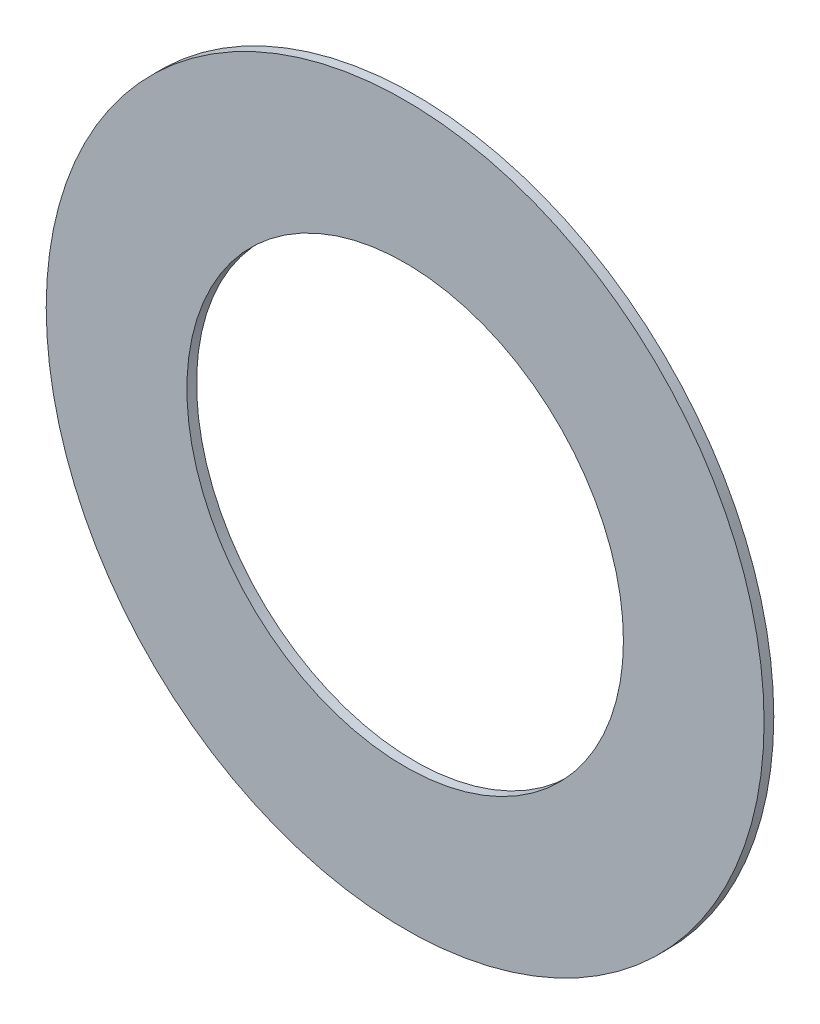
SolidWorks part; units mm, degrees
material "А1 ГОСТ 9347-74"
ref_plane "Спереди" through (0, 0, 0) normal (0, 0, 1) x (1, 0, 0)
ref_plane "Сверху" through (0, 0, 0) normal (0, 1, 0) x (1, 0, 0)
ref_plane "Справа" through (0, 0, 0) normal (1, 0, 0) x (0, 0, -1)
sketch "Эскиз1" plane through (0, 0, 0) normal (0, 0, 1) x (1, 0, 0)
  circle A0 centre (0, 0) radius 37
  circle A1 centre (0, 0) radius 22.5
  dimension "D1" = 74
  dimension "D2" = 45
extrude "Бобышка-Вытянуть1" add sketch "Эскиз1" along normal blind 1
